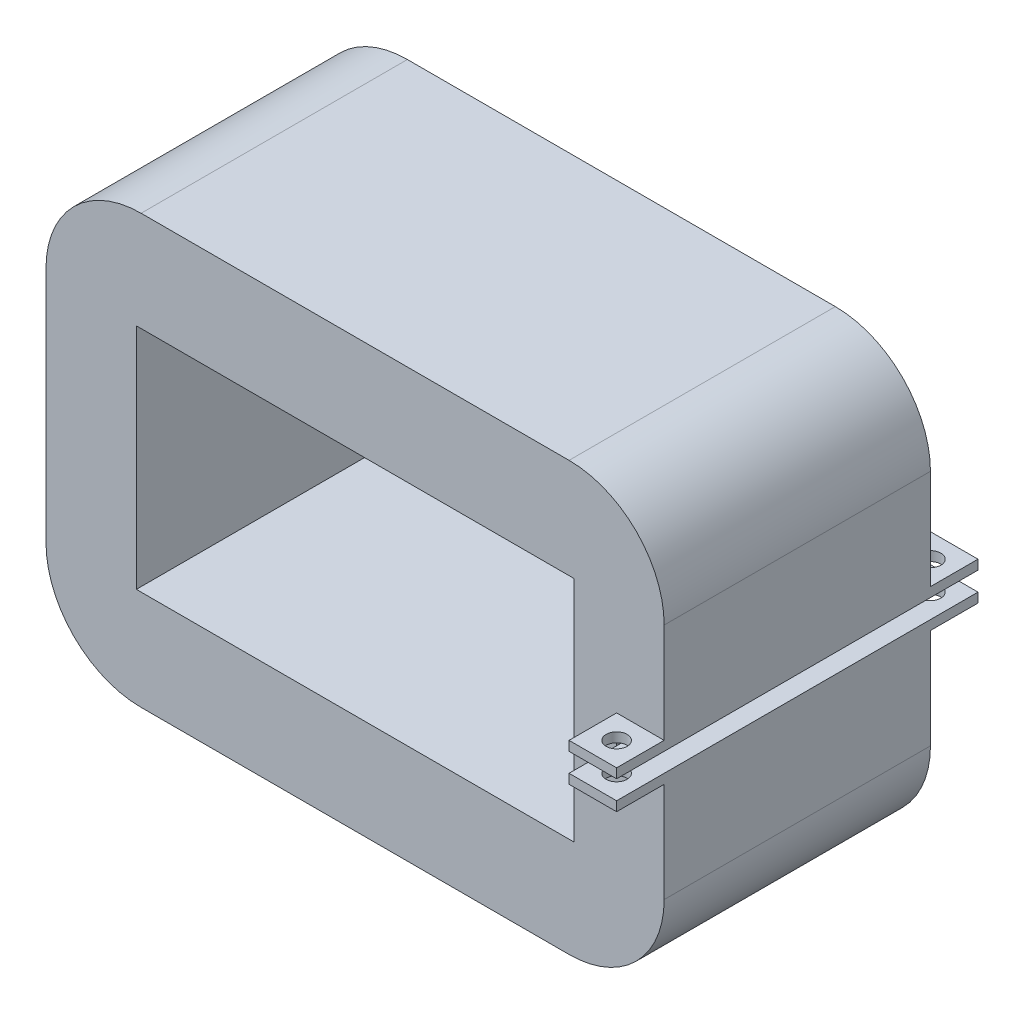
SolidWorks part; units mm, degrees
ref_plane "前基準面" through (0, 0, 0) normal (0, 0, 1) x (1, 0, 0)
ref_plane "上基準面" through (0, 0, 0) normal (0, 1, 0) x (1, 0, 0)
ref_plane "右基準面" through (0, 0, 0) normal (1, 0, 0) x (0, 0, -1)
sketch "草圖1" plane through (0, 0, 0) normal (0, 0, 1) x (1, 0, 0)
  line L0 (-9.02, 0) -> (7.9922, 0) construction
  line L2 (-59.9347, 22.5) -> (5.0653, 22.5)
  line L3 (-59.9347, 22.5) -> (-59.9347, -22.5)
  line L4 (-59.9347, -22.5) -> (5.0653, -22.5)
  line L5 (5.0653, 22.5) -> (5.0653, -22.5)
  dimension "D1" = 45
  dimension "D2" = 22.5
  dimension "D3" = 65
extrude "填料-伸長1" add sketch "草圖1" along normal blind 28
sketch "草圖2" plane through (0, 0, 0) normal (0, 0, 1) x (1, 0, 0)
  line L0 (-59.9347, 0) -> (5.361, 0) construction
  line L1 (-59.9347, 22.5) -> (-59.9347, -22.5) construction
  line L2 (-27.4347, 22.5) -> (-27.4347, -22.5) construction
  line L3 (5.0653, 22.5) -> (-59.9347, 22.5) construction
  line L4 (-59.9347, -22.5) -> (5.0653, -22.5) construction
  line L6 (-50.4347, 12) -> (-4.4347, 12)
  line L7 (-50.4347, 12) -> (-50.4347, -12)
  line L8 (-50.4347, -12) -> (-4.4347, -12)
  line L9 (-4.4347, 12) -> (-4.4347, -12)
  dimension "D1" = 46
  dimension "D2" = 24
  dimension "D3" = 9.5
  dimension "D4" = 10.5
extrude "除料-伸長1" cut sketch "草圖2" along normal blind 39
ref_plane "平面1" through (0, 0, 28) normal (0, 0, 1) x (1, 0, 0)
sketch "草圖3" plane through (0, 0, 28) normal (0, 0, 1) x (1, 0, 0)
  line L0 (-59.9347, 22.5) -> (-59.9347, -22.5) construction
  line L2 (-59.9347, 12) -> (-55.9347, 12)
  line L3 (-59.9347, 12) -> (-59.9347, -12)
  line L4 (-59.9347, -12) -> (-55.9347, -12)
  line L5 (-55.9347, 12) -> (-55.9347, -12)
  line L6 (-50.4347, 12) -> (-4.4347, 12) construction
  dimension "D1" = 4
  dimension "D2" = 24
  dimension "D3" = 0
ref_plane "平面2" through (-59.9347, 0, 0) normal (-1, 0, 0) x (0, 0, 1)
sketch "草圖6" plane through (0, 0, 28) normal (0, 0, 1) x (1, 0, 0)
  line L0 (-14.4347, 0) -> (5.0653, -22.5)
  line L1 (-4.4347, 12) -> (-4.4347, -12) construction
  line L2 (-4.4347, -12) -> (-50.4347, -12) construction
  line L3 (-14.4347, 0) -> (-14.4347, -22.5)
  line L4 (-59.9347, -22.5) -> (5.0653, -22.5) construction
  line L5 (-14.4347, -22.5) -> (5.0653, -22.5)
  dimension "D1" = 10
  dimension "D2" = 12
ref_plane "平面4" through (0, 0, 0) normal (0, 0, -1) x (-1, 0, 0)
fillet "圓角1" radius 10 1 edges at (-59.9347, -22.5, 14)
fillet "圓角2" radius 10 1 edges at (-59.9347, 22.5, 14)
fillet "圓角3" radius 10 1 edges at (5.0653, 22.5, 14)
fillet "圓角4" radius 10 1 edges at (5.0653, -22.5, 14)
ref_plane "平面5" through (0, 0, 0) normal (0, 1, 0) x (1, 0, 0)
sketch "草圖9" plane through (0, 0, 0) normal (0, 1, 0) x (1, 0, 0)
  line L0 (5.0653, 0) -> (5.0653, -28) construction
  line L1 (0.0653, 3.3121) -> (5.0653, 3.3121)
  line L2 (0.0653, 3.3121) -> (0.0653, -30.7585)
  line L3 (0.0653, -30.7585) -> (5.0653, -30.7585)
  line L4 (5.0653, 3.3121) -> (5.0653, -30.7585)
  dimension "D1" = 5
  dimension "D2" = 5
  dimension "D3" = 34.0706
extrude "除料-伸長2" cut sketch "草圖9" against normal blind 1 and the other way blind 1
sketch "草圖10" plane through (0, 0, 0) normal (0, 0, 1) x (1, 0, 0)
  line L0 (5.0653, -12.5) -> (5.0653, -1) construction
  line L1 (0.0653, -1) -> (5.0653, -1)
  line L2 (0.0653, -1) -> (0.0653, -2)
  line L3 (0.0653, -2) -> (5.0653, -2)
  line L4 (5.0653, -1) -> (5.0653, -2)
  line L5 (5.0653, 1) -> (5.0653, 12.5) construction
  line L6 (0.0653, 1) -> (5.0653, 1)
  line L7 (0.0653, 1) -> (0.0653, 2)
  line L8 (0.0653, 2) -> (5.0653, 2)
  line L9 (5.0653, 1) -> (5.0653, 2)
  dimension "D1" = 1
  dimension "D2" = 1
extrude "填料-伸長5" add sketch "草圖10" against normal blind 5
ref_plane "平面6" through (0, -2, 0) normal (0, -1, 0) x (-1, 0, 0)
sketch "草圖12" plane through (0, -2, 0) normal (0, -1, 0) x (-1, 0, 0)
  line L0 (-5.0653, 2.5) -> (-0.0653, 2.5) construction
  line L1 (-5.0653, 5) -> (-5.0653, 0) construction
  line L2 (-0.0653, 5) -> (-0.0653, 0) construction
  line L3 (-2.5653, 5) -> (-2.5653, 0) construction
  line L4 (-0.0653, 5) -> (-5.0653, 5) construction
  line L5 (24.75, 0) -> (-24.75, 0) construction
  circle A0 centre (-2.5653, 2.5) radius 1.1
  dimension "D1" = 2.2
extrude "除料-伸長3" cut sketch "草圖12" against normal blind 5 contours A0
pattern_linear "直線複製排列1" count 2 spacing 33 along (0, 0, 1) of "填料-伸長5"
pattern_linear "直線複製排列2" count 2 spacing 33 along (0, 0, 1) of "除料-伸長3"
